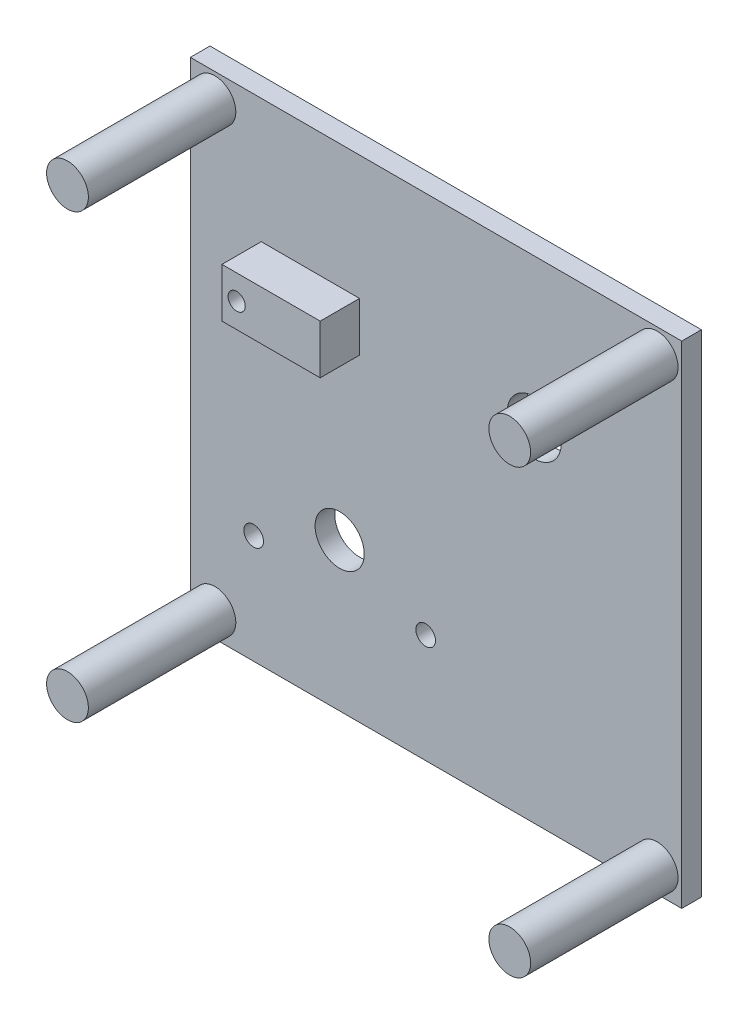
SolidWorks part; units mm, degrees
ref_plane "Front Plane" through (0, 0, 0) normal (0, 0, 1) x (1, 0, 0)
ref_plane "Top Plane" through (0, 0, 0) normal (0, 1, 0) x (1, 0, 0)
ref_plane "Right Plane" through (0, 0, 0) normal (1, 0, 0) x (0, 0, -1)
sketch "Sketch1" plane through (0, 0, 0) normal (0, 0, 1) x (1, 0, 0)
  line L1 (-50, -50) -> (50, -50)
  line L2 (-50, -50) -> (-50, 50)
  line L3 (-50, 50) -> (50, 50)
  line L4 (50, -50) -> (50, 50)
  line L5 (-50, -50) -> (50, 50) construction
  line L6 (-50, 50) -> (50, -50) construction
  point P0 (0, 0)
  dimension "D1" = 100
  dimension "D2" = 100
extrude "Boss-Extrude1" add sketch "Sketch1" along normal blind 4
sketch "Sketch2" plane through (0, 0, 4) normal (0, 0, 1) x (1, 0, 0)
  line L0 (50, 50) -> (-50, 50) construction
  line L2 (50, -50) -> (50, 50) construction
  line L3 (-50, 50) -> (-50, -50) construction
  line L4 (-50, -50) -> (50, -50) construction
  circle A0 centre (45, 45) radius 4.25
  circle A1 centre (-45, 45) radius 4.25
  circle A2 centre (-45, -45) radius 4.25
  circle A3 centre (45, -45) radius 4.25
  dimension "D5" = 8.5
  dimension "D1" = 5
  dimension "D2" = 5
  dimension "D3" = 5
  dimension "D4" = 5
extrude "Boss-Extrude2" add sketch "Sketch2" along normal blind 30
sketch "Sketch4" plane through (0, 0, 0) normal (0, 0, -1) x (-1, 0, 0)
  circle A2 centre (-45, 45) radius 4.75
  circle A3 centre (-45, 45) radius 4.75
  circle A5 centre (45, 45) radius 4.75
  circle A6 centre (45, 45) radius 4.75
  circle A8 centre (-45, -45) radius 4.75
  circle A9 centre (-45, -45) radius 4.75
  circle A11 centre (45, -45) radius 4.75
  circle A12 centre (45, -45) radius 4.75
  dimension "D1" = 0.5
  dimension "D2" = 0.5
  dimension "D3" = 0.5
  dimension "D4" = 0.5
extrude "Cut-Extrude1" cut sketch "Sketch4" against normal blind 1.5
extrude "Cut-Extrude2" cut sketch "Sketch5" against normal through all both and the other way through all
sketch "Sketch5" plane through (-38.4043, -79.6142, 4) normal (0, 0, 1) x (1, 0, 0)
  circle A2 centre (36.2926, 51.7502) radius 2
  circle A3 centre (1.2926, 51.7502) radius 2
  circle A7 centre (18.7926, 59.7502) radius 5
sketch "Sketch6" plane through (0, 0, 4) normal (0, 0, 1) x (1, 0, 0)
  line L0 (19.9832, 19.731) -> (-44.0452, 19.731) construction
  line L1 (-35.5712, 14.731) -> (-15.5712, 14.731)
  line L2 (-35.5712, 14.731) -> (-35.5712, 24.731)
  line L3 (-35.5712, 24.731) -> (-15.5712, 24.731)
  line L4 (-15.5712, 14.731) -> (-15.5712, 24.731)
  line L5 (-35.5712, 14.731) -> (-15.5712, 24.731) construction
  line L6 (-35.5712, 24.731) -> (-15.5712, 14.731) construction
  circle A0 centre (-32.5712, 19.731) radius 1.75
  point P0 (-25.5712, 19.731)
  dimension "D1" = 3.5
  dimension "D2" = 20
  dimension "D3" = 10
  dimension "D4" = 3
extrude "Boss-Extrude3" add sketch "Sketch6" along normal blind 8
extrude "Cut-Extrude3" cut sketch "Sketch7" against normal blind 8
sketch "Sketch7" plane through (-38.4043, -79.6142, 0) normal (0, 0, -1) x (-1, 0, 0)
  circle A3 centre (-58.3876, 99.3452) radius 5.5
